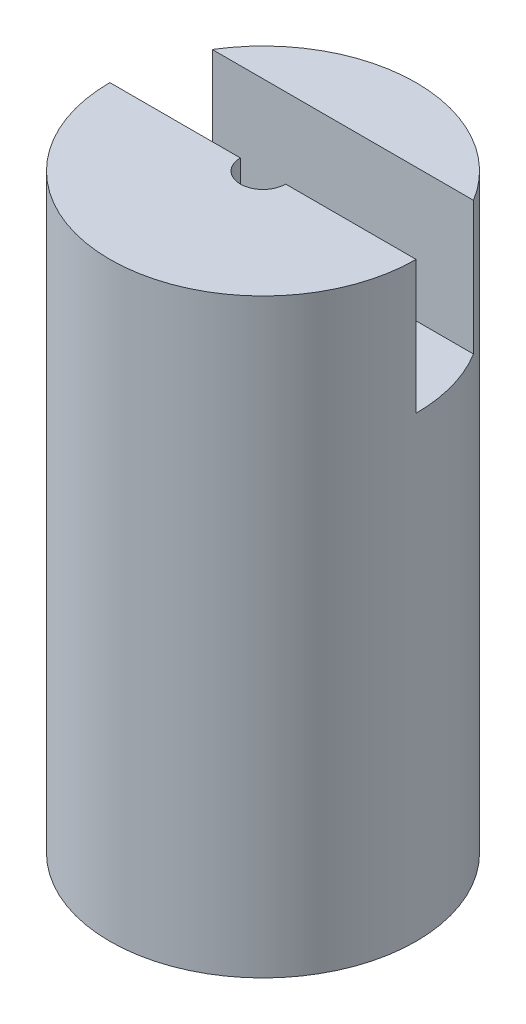
SolidWorks part; units mm, degrees
ref_plane "Спереди" through (0, 0, 0) normal (0, 0, 1) x (1, 0, 0)
ref_plane "Сверху" through (0, 0, 0) normal (0, 1, 0) x (1, 0, 0)
ref_plane "Справа" through (0, 0, 0) normal (1, 0, 0) x (0, 0, -1)
sketch "Эскиз1" plane through (0, 0, 0) normal (1, 0, 0) x (0, 0, -1)
  line L5 (2.25, 26.3879) -> (0, 26.3879)
  line L6 (0, 26.3879) -> (0, -1.1917)
  line L7 (0, -1.1917) -> (17.25, -1.1917)
  line L8 (17.25, -1.1917) -> (17.25, 65.3402)
  line L9 (17.25, 65.3402) -> (2.55, 65.3402)
  line L10 (0, 93.4641) -> (0, -18.7269) construction
  line L11 (2.25, 26.3879) -> (2.25, 50.3402)
  line L12 (1.6612, 50.3402) -> (8, 50.3402) construction
  line L13 (2.25, 50.3402) -> (2.55, 50.3402)
  line L14 (2.55, 65.3402) -> (2.55, 50.3402)
revolve "Повернуть1" add sketch "Эскиз1" angle 360 about L10
sketch "Эскиз2" plane through (0, 0, 0) normal (0, 0, 1) x (1, 0, 0)
  line L5 (17.25, 65.3402) -> (-17.25, 65.3402) construction
  line L6 (-21.8122, 80.3402) -> (21.8122, 80.3402)
  line L7 (2.55, 65.3402) -> (-2.55, 65.3402) construction
  line L8 (-21.8122, 80.3402) -> (-21.8122, 50.3402)
  line L9 (-21.8122, 50.3402) -> (21.8122, 50.3402)
  line L10 (21.8122, 80.3402) -> (21.8122, 50.3402)
  line L11 (-21.8122, 80.3402) -> (21.8122, 50.3402) construction
  line L12 (-21.8122, 50.3402) -> (21.8122, 80.3402) construction
  point P0 (0, 65.3402)
  point P1 (0, 65.3402)
extrude "Вырез-Вытянуть1" cut sketch "Эскиз2" against normal blind 9
